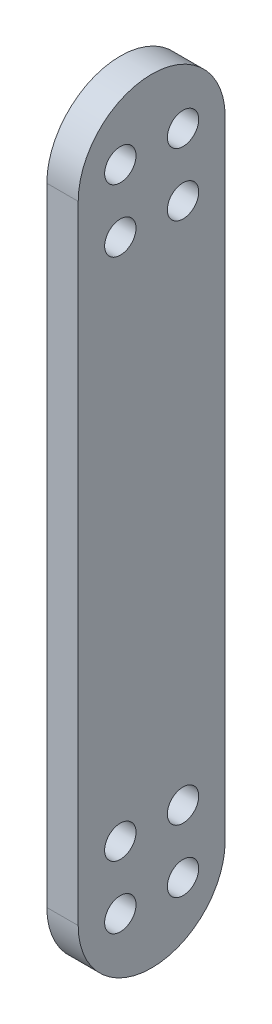
SolidWorks part; units mm, degrees
material "ABS"
ref_plane "Plano frontal" through (0, 0, 0) normal (0, 0, 1) x (1, 0, 0)
ref_plane "Plano superior" through (0, 0, 0) normal (0, 1, 0) x (1, 0, 0)
ref_plane "Plano direito" through (0, 0, 0) normal (1, 0, 0) x (0, 0, -1)
sketch "Esboço1" plane through (0, 0, 0) normal (0, 0, 1) x (1, 0, 0)
  line L0 (0, 0) -> (0, 50)
  line L1 (0, 50) -> (10, 50)
  line L2 (10, 50) -> (10, 10)
  line L3 (10, 10) -> (40, 10)
  line L4 (40, 10) -> (40, 50)
  line L5 (40, 50) -> (50, 50)
  line L6 (50, 50) -> (50, 0)
  line L7 (50, 0) -> (0, 0)
  dimension "D1" = 10
  dimension "D2" = 30
  dimension "D3" = 50
  dimension "D4" = 40
extrude "Ressalto-extrusão1" add sketch "Esboço1" along normal blind 40
sketch "Esboço2" plane through (0, 0, 0) normal (-1, 0, 0) x (0, 0, 1)
  line L0 (20, 50) -> (20, 17.3959) construction
  line L1 (40, 50) -> (0, 50) construction
  circle A1 centre (20, 33.698) radius 5
  dimension "D1" = 10
extrude "Corte-extrusão1" cut sketch "Esboço2" against normal through all
sketch "Esboço3" plane through (0, 0, 0) normal (-1, 0, 0) x (0, 0, 1)
  line L0 (8.2847, 33.698) -> (8.2847, 133.698)
  line L1 (8.2847, 83.698) -> (43.0317, 83.698) construction
  line L2 (31.7153, 133.698) -> (31.7153, 33.698)
  line L3 (17.5, 125.4132) -> (22.5, 125.4132)
  line L4 (15, 127.9132) -> (15, 132.9132)
  line L5 (17.5, 135.4132) -> (22.5, 135.4132)
  line L6 (25, 127.9132) -> (25, 132.9132)
  line L7 (25, 39.4827) -> (25, 34.4827)
  line L8 (17.5, 31.9827) -> (22.5, 31.9827)
  line L9 (15, 39.4827) -> (15, 34.4827)
  line L10 (17.5, 41.9827) -> (22.5, 41.9827)
  arc A0 (8.2847, 33.698) -> (31.7153, 33.698) centre (20, 33.698) ccw
  arc A1 (31.7153, 133.698) -> (8.2847, 133.698) centre (20, 133.698) ccw
  circle A3 centre (15, 135.4132) radius 2.5
  circle A5 centre (25, 135.4132) radius 2.5
  circle A6 centre (25, 125.4132) radius 2.5
  circle A7 centre (15, 125.4132) radius 2.5
  circle A8 centre (25, 31.9827) radius 2.5
  circle A9 centre (25, 41.9827) radius 2.5
  circle A10 centre (15, 41.9827) radius 2.5
  circle A11 centre (15, 31.9827) radius 2.5
  arc A12 (31.7153, 33.698) -> (8.2847, 33.698) centre (20, 33.698) cw
  point P17 (20, 145.4132)
  circle M5 centre (20, 33.698) radius 5
  line M9 (40, 50) -> (0, 50)
  dimension "D1" = 5
  dimension "D2" = 100
  dimension "D3" = 10
extrude "Ressalto-extrusão2" add sketch "Esboço3" along normal blind 5 contours L0 A0 L2 A11 L9 A10 L10 A9 L7 A8 M9 M5 | L9 A11 A8 L7 A9 L10 A10 M5 | A11 L8 A8 M5 | L8 A11 A8 M5 | L1 L0 L2 M9 | L0 L1 L2 A1 A7 L4 A3 L5 A5 L6 A6 L3 | A7 L3 A6 L6 A5 L5 A3 L4
sketch "Esboço4" plane through (50, 0, 0) normal (1, 0, 0) x (0, 0, -1)
  line L1 (-49.9083, -8.4551) -> (30.2499, -8.4551)
  line L2 (-49.9083, -8.4551) -> (-49.9083, 67.6326)
  line L3 (-49.9083, 67.6326) -> (30.2499, 67.6326)
  line L4 (30.2499, -8.4551) -> (30.2499, 67.6326)
extrude "Corte-extrusão2" cut sketch "Esboço4" against normal up to surface (50 mm away) up to face at (0, 125.4132, 27.5)
